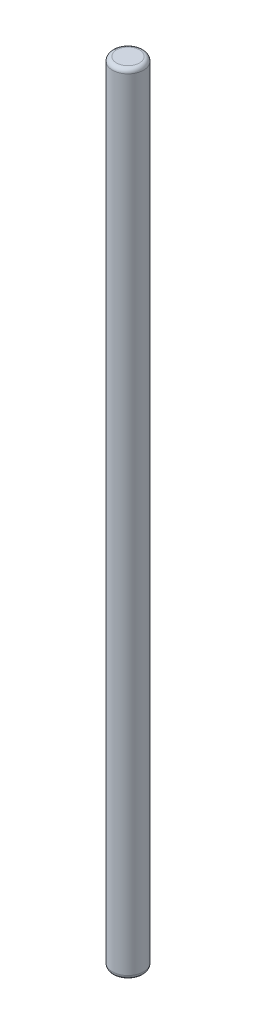
SolidWorks part; units mm, degrees
ref_plane "Plan de face" through (0, 0, 0) normal (0, 0, 1) x (1, 0, 0)
ref_plane "Plan de dessus" through (0, 0, 0) normal (0, 1, 0) x (1, 0, 0)
ref_plane "Plan de droite" through (0, 0, 0) normal (1, 0, 0) x (0, 0, -1)
sketch "Esquisse1" plane through (0, 0, 0) normal (0, 1, 0) x (1, 0, 0)
  circle A0 centre (0, 0) radius 0.75
  dimension "D1" = 1.5
extrude "Extrusion1" add sketch "Esquisse1" along normal blind 38
fillet "Congé1" radius 0.2 2 edges at (0, 0, 0.75) (0, 38, 0.75)
